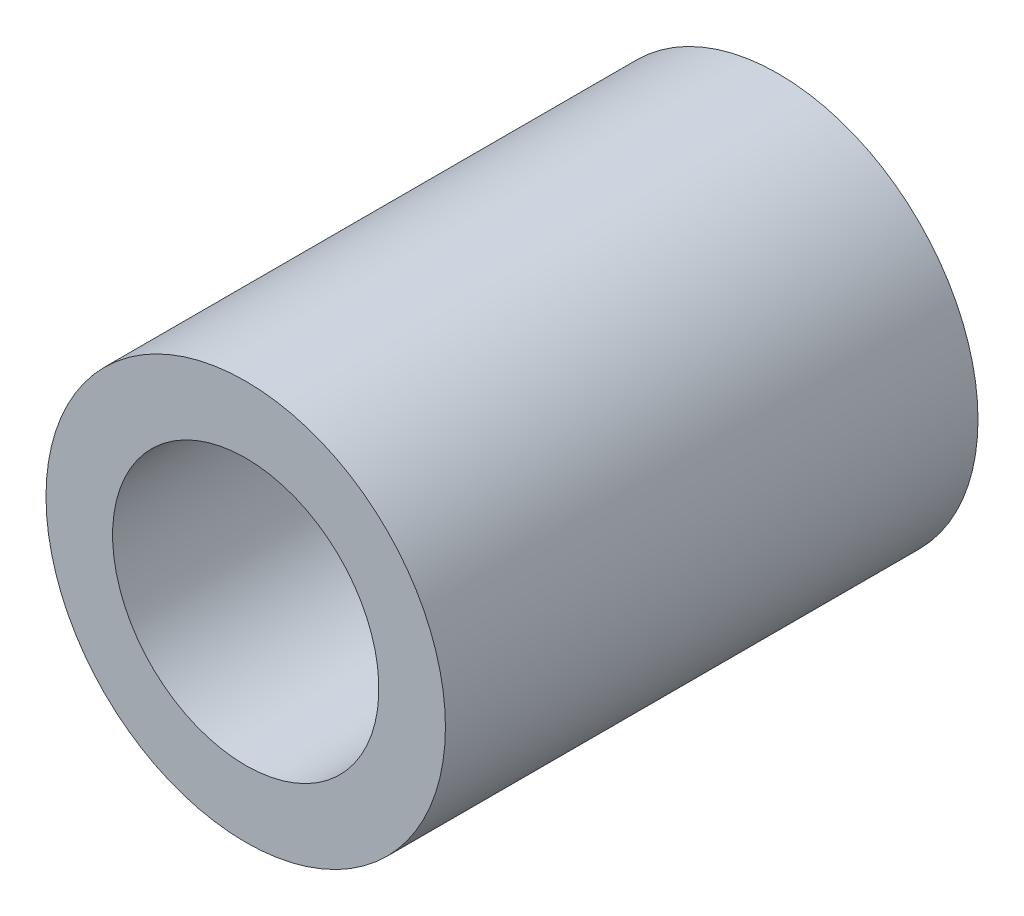
SolidWorks part; units mm, degrees
material "Commercial Bronze, UNS C22000 (90-10 Bronze)"
ref_plane "Front" through (0, 0, 0) normal (0, 0, 1) x (1, 0, 0)
ref_plane "Top" through (0, 0, 0) normal (0, 1, 0) x (1, 0, 0)
ref_plane "Right" through (0, 0, 0) normal (1, 0, 0) x (0, 0, -1)
sketch "Sketch1" plane through (0, 0, 0) normal (1, 0, 0) x (0, 0, -1)
  line L0 (0, 0) -> (0, -22.2788) construction
  line L1 (-15.185, 0) -> (15.185, 0) construction
  line L2 (-12.7, -6.35) -> (12.7, -6.35)
  line L3 (-12.7, -6.35) -> (-12.7, -9.525)
  line L4 (-12.7, -9.525) -> (12.7, -9.525)
  line L5 (12.7, -6.35) -> (12.7, -9.525)
  line L6 (-12.7, -6.35) -> (12.7, -9.525) construction
  line L7 (-12.7, -9.525) -> (12.7, -6.35) construction
  point P2 (0, -7.9375)
  dimension "D1" = 3.175
  dimension "D2" = 19.05
  dimension "D3" = 25.4
revolve "Revolve1" add sketch "Sketch1" angle 360 about L1
